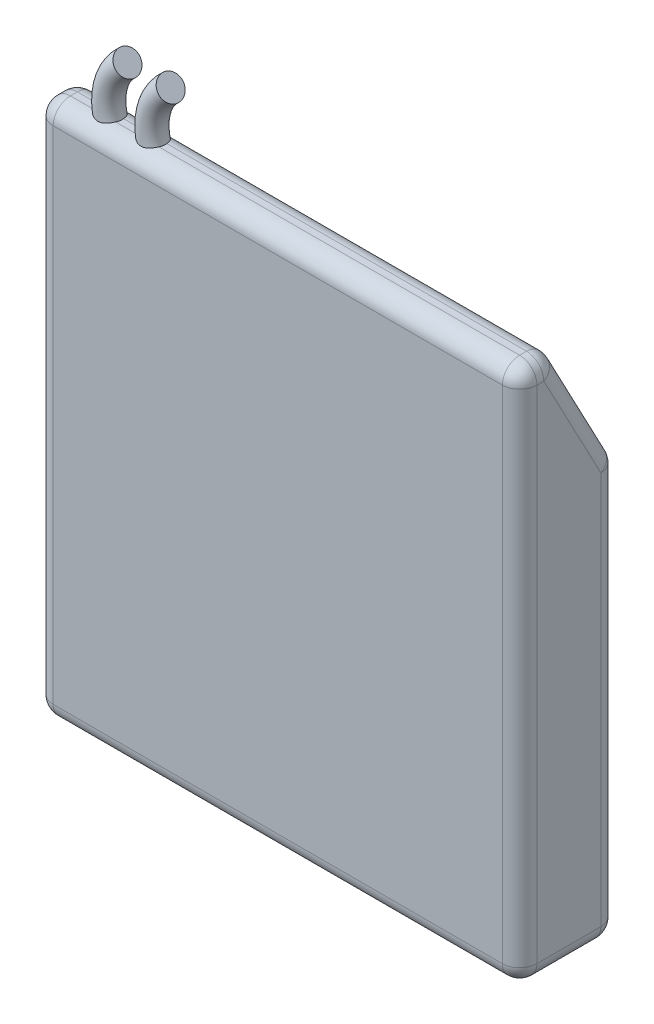
SolidWorks part; units mm, degrees
ref_plane "前视基准面" through (0, 0, 0) normal (0, 0, 1) x (1, 0, 0)
ref_plane "上视基准面" through (0, 0, 0) normal (0, 1, 0) x (1, 0, 0)
ref_plane "右视基准面" through (0, 0, 0) normal (1, 0, 0) x (0, 0, -1)
sketch "草图1" plane through (0, 0, 0) normal (1, 0, 0) x (0, 0, -1)
  line L0 (0, 0) -> (0, 31)
  line L1 (0, 31) -> (2, 31)
  line L2 (2, 31) -> (5.7, 24)
  line L3 (5.7, 24) -> (5.7, 0)
  line L4 (5.7, 0) -> (0, 0)
  dimension "D1" = 5.7
  dimension "D2" = 31
  dimension "D3" = 2
  dimension "D4" = 24
extrude "凸台-拉伸1" add sketch "草图1" along normal blind 28
fillet "圆角1" radius 1 15 edges at (14, 0, -5.7) (14, 24, -5.7) (14, 31, -2) (14, 31, 0) (14, 0, 0) (28, 15.5, 0) (28, 31, -1) (28, 27.5, -3.85) (28, 12, -5.7) (28, 0, -2.85) (0, 15.5, 0) (0, 31, -1) (0, 27.5, -3.85) (0, 12, -5.7) (0, 0, -2.85)
ref_plane "基准面1" through (0, 0, -1.3) normal (0, 0, 1) x (1, 0, 0)
sketch "草图2" plane through (0, 0, -1.3) normal (0, 0, 1) x (1, 0, 0)
  arc A0 (4.0017, 34.0193) -> (4.58, 28.7579) centre (6.1669, 31.5948) ccw
  point P3 (4.0017, 34.0193)
sweep "扫描1" add path "草图2" circular profile diameter 1.4 parameters "D3"=1.4
pattern_linear "阵列(线性)1" count 2 spacing 2.5 along (1, 0, 0) of "扫描1"
